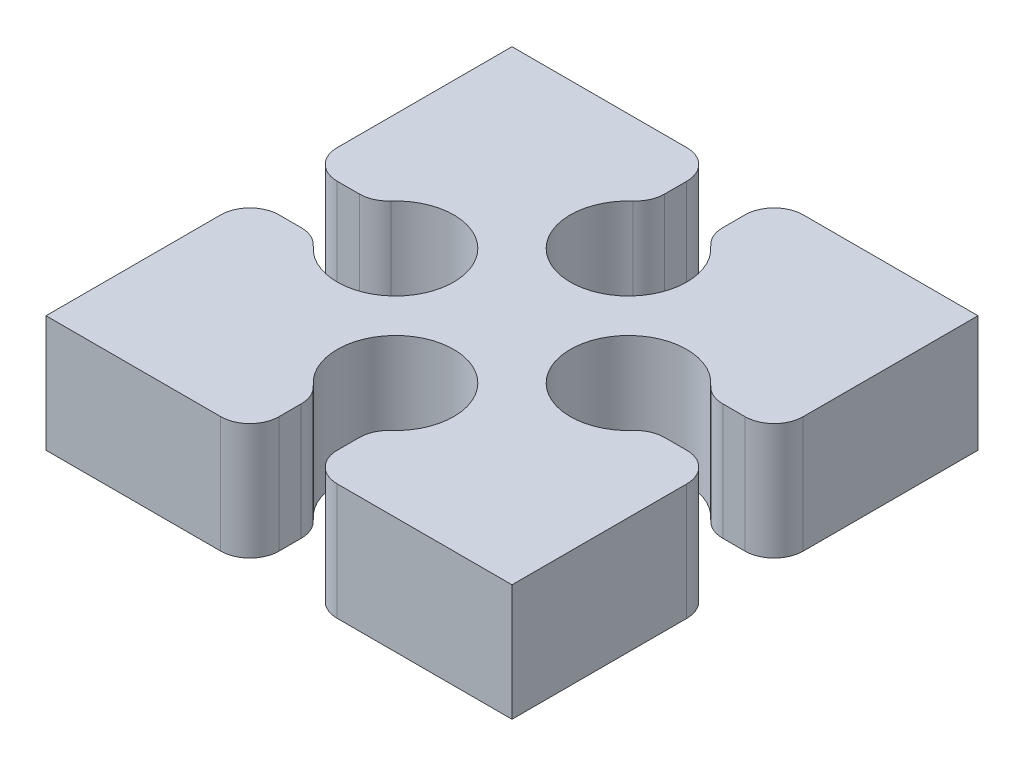
SolidWorks part; units mm, degrees
ref_plane "Front Plane" through (0, 0, 0) normal (0, 0, 1) x (1, 0, 0)
ref_plane "Top Plane" through (0, 0, 0) normal (0, 1, 0) x (1, 0, 0)
ref_plane "Right Plane" through (0, 0, 0) normal (1, 0, 0) x (0, 0, -1)
sketch "Sketch1" plane through (0, 0, 0) normal (0, 1, 0) x (1, 0, 0)
  line L0 (-4, 4) -> (4, -4) construction
  line L1 (-4, 4) -> (4, 4)
  line L2 (-4, 4) -> (-4, -4)
  line L3 (-4, -4) -> (4, -4)
  line L4 (4, 4) -> (4, -4)
  line L5 (4, 4) -> (-4, -4) construction
  line L6 (0, -28.0996) -> (0, 28.0996) construction
  line L7 (0, 4) -> (0, 2)
  line L8 (4, 0.5) -> (2, 0.5)
  line L9 (-0.5, 4) -> (0.5, 4)
  line L10 (-0.5, 4) -> (-0.5, 2)
  line L11 (-0.5, 2) -> (0.5, 2)
  line L12 (0.5, 4) -> (0.5, 2)
  line L13 (4, 0.5) -> (4, -0.5)
  line L14 (4, -0.5) -> (2, -0.5)
  line L15 (2, 0.5) -> (2, -0.5)
  line L16 (0.5, -4) -> (0.5, -2)
  line L17 (0.5, -4) -> (-0.5, -4)
  line L18 (-0.5, -4) -> (-0.5, -2)
  line L19 (0.5, -2) -> (-0.5, -2)
  line L20 (-4, -0.5) -> (-2, -0.5)
  line L21 (-4, -0.5) -> (-4, 0.5)
  line L22 (-4, 0.5) -> (-2, 0.5)
  line L23 (-2, -0.5) -> (-2, 0.5)
  circle A0 centre (0, 2) radius 1
  circle A1 centre (2, 0) radius 1
  circle A2 centre (0, -2) radius 1
  circle A3 centre (-2, 0) radius 1
  point P4 (0, 0)
  point P16 (0, 2)
  point P37 (0, 0)
  dimension "D3" = 2
  dimension "D1" = 8
  dimension "D2" = 8
  dimension "D4" = 2
  dimension "D5" = 1
  dimension "D6" = 4
extrude "Boss-Extrude1" add sketch "Sketch1" along normal blind 2 contours A3 L20 L2 L3 L18 A2 L16 L4 L14 A1 L8 L1 L12 A0 L10 L22
fillet "Fillet1" radius 0.5 16 edges at (-2.866, 1, -0.5) (-2.866, 1, 0.5) (0.5, 1, 2.866) (-0.5, 1, 2.866) (2.866, 1, 0.5) (2.866, 1, -0.5) (0.5, 1, -2.866) (-0.5, 1, -2.866) (0.5, 1, 4) (-0.5, 1, 4) (4, 1, 0.5) (4, 1, -0.5) (0.5, 1, -4) (-0.5, 1, -4) (-4, 1, 0.5) (-4, 1, -0.5)
equation "\"length\"= 8"
equation "\"D1@Sketch1\"= \"length\""
equation "\"D2@Sketch1\"= \"length\""
